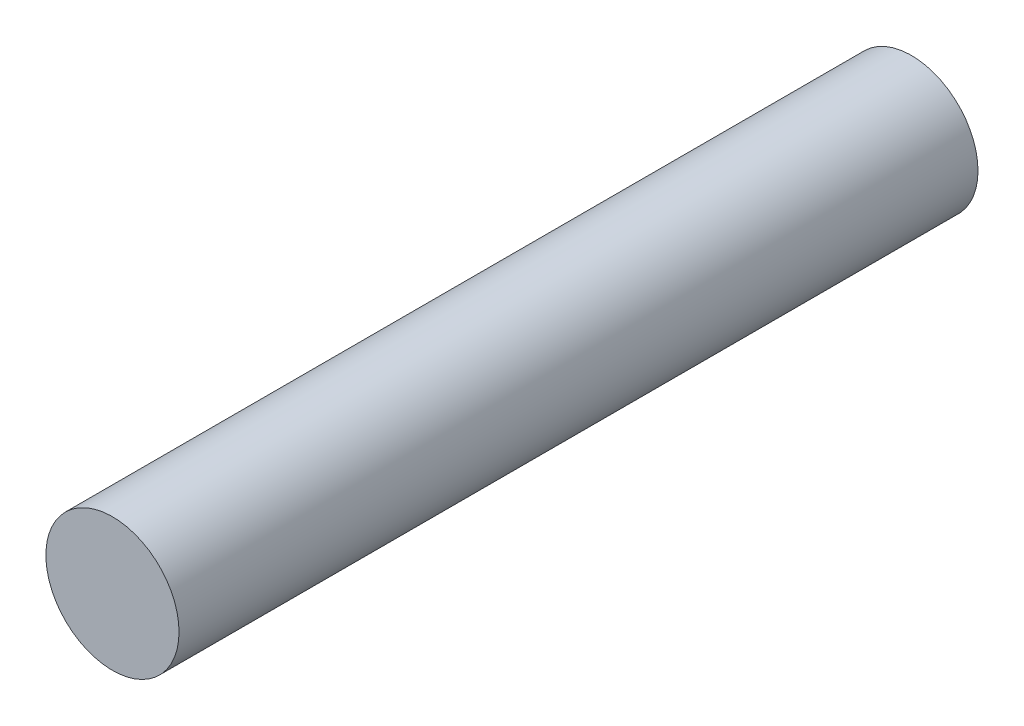
SolidWorks part; units mm, degrees
ref_plane "Front" through (0, 0, 0) normal (0, 0, 1) x (1, 0, 0)
ref_plane "Top" through (0, 0, 0) normal (0, 1, 0) x (1, 0, 0)
ref_plane "Right" through (0, 0, 0) normal (1, 0, 0) x (0, 0, -1)
sketch "Sketch1" plane through (0, 0, 0) normal (0, 0, 1) x (1, 0, 0)
  circle A0 centre (-5.9147, 4.8999) radius 6.35
  dimension "D1" = 12.7
extrude "Boss-Extrude1" add sketch "Sketch1" along normal blind 76.2
sketch "Sketch3" plane through (0, 0, 0) normal (0, 0, -1) x (-1, 0, 0)
  circle A0 centre (5.9147, 4.8999) radius 4.7625
  dimension "D1" = 9.525
extrude "Cut-Extrude1" cut sketch "Sketch3" against normal blind 31.75
